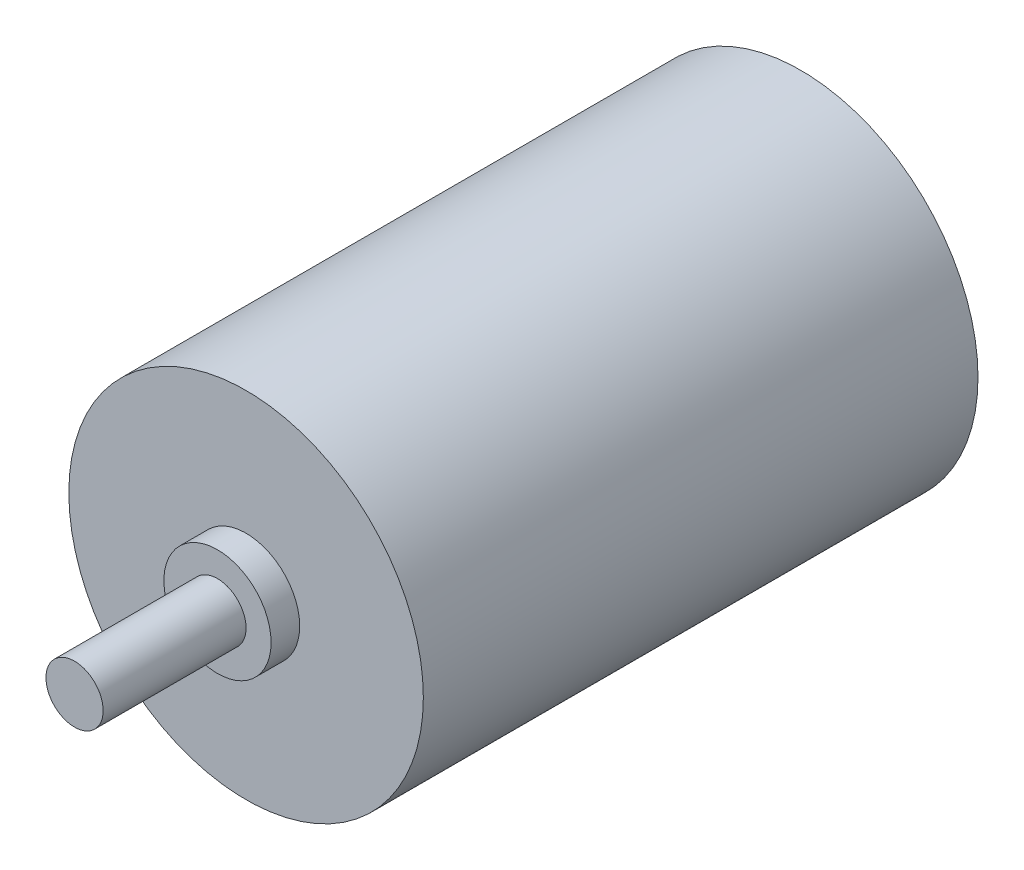
SolidWorks part; units mm, degrees
ref_plane "Ebene vorne" through (0, 0, 0) normal (0, 0, 1) x (1, 0, 0)
ref_plane "Ebene oben" through (0, 0, 0) normal (0, 1, 0) x (1, 0, 0)
ref_plane "Ebene rechts" through (0, 0, 0) normal (1, 0, 0) x (0, 0, -1)
sketch "Skizze1" plane through (0, 0, 0) normal (0, 0, 1) x (1, 0, 0)
  circle A0 centre (0, 0) radius 12.4
  dimension "D1" = 24.8
extrude "Aufsatz-Linear austragen1" add sketch "Skizze1" along normal blind 38.8
sketch "Skizze2" plane through (0, 0, 38.8) normal (0, 0, 1) x (1, 0, 0)
  circle A0 centre (0, 0) radius 3.75
  dimension "D1" = 7.5
extrude "Aufsatz-Linear austragen2" add sketch "Skizze2" along normal blind 2
sketch "Skizze3" plane through (0, 0, 40.8) normal (0, 0, 1) x (1, 0, 0)
  circle A0 centre (0, 0) radius 2
  dimension "D1" = 4
extrude "Aufsatz-Linear austragen3" add sketch "Skizze3" along normal blind 10
sketch "Skizze4" plane through (0, 0, 0) normal (0, 0, -1) x (-1, 0, 0)
  line L0 (0, -9) -> (0, 0) construction
  line L1 (3.5, -8) -> (-3.5, -8)
  line L2 (3.5, -8) -> (3.5, -10)
  line L3 (3.5, -10) -> (-3.5, -10)
  line L4 (-3.5, -8) -> (-3.5, -10)
  line L5 (3.5, -8) -> (-3.5, -10) construction
  line L6 (3.5, -10) -> (-3.5, -8) construction
  point P0 (0, -9)
  dimension "D1" = 7
  dimension "D2" = 9
  dimension "D3" = 2
extrude "Aufsatz-Linear austragen4" add sketch "Skizze4" along normal blind 3
